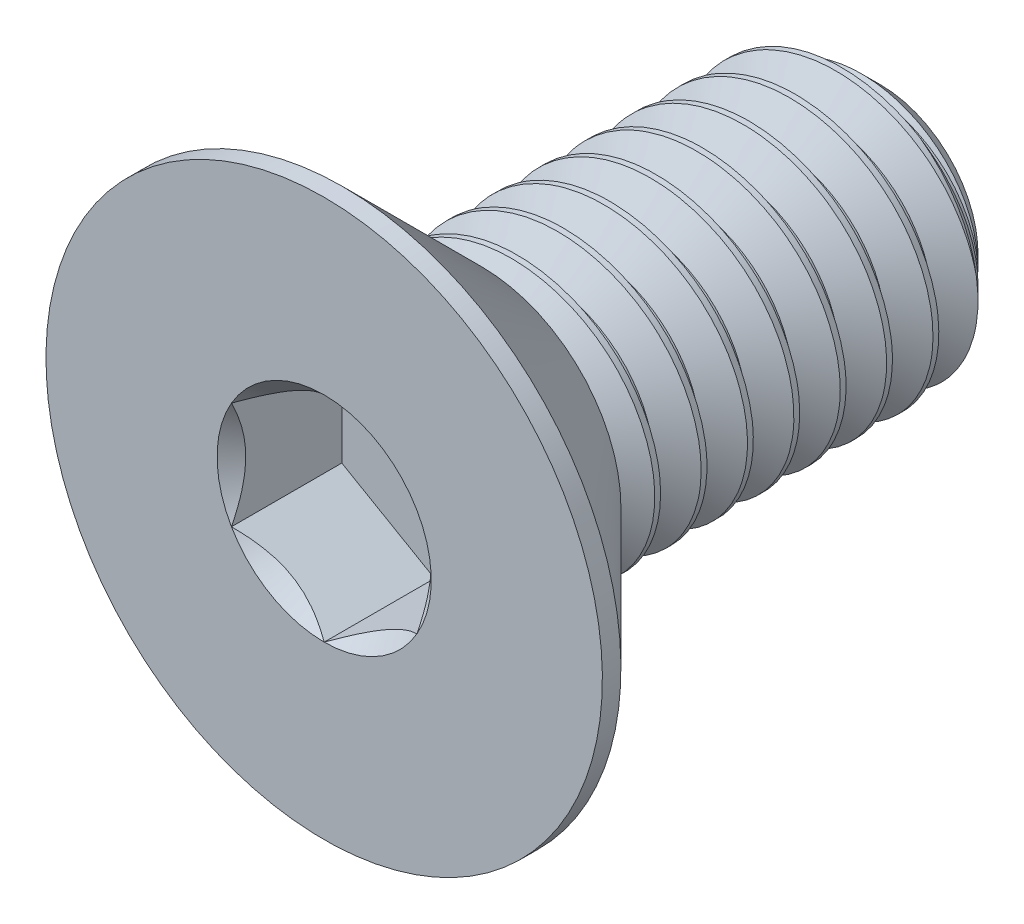
SolidWorks part; units mm, degrees
ref_plane "Front" through (0, 0, 0) normal (0, 0, 1) x (1, 0, 0)
ref_plane "Top" through (0, 0, 0) normal (0, 1, 0) x (1, 0, 0)
ref_plane "Right" through (0, 0, 0) normal (1, 0, 0) x (0, 0, -1)
sketch "Sketch1" plane through (0, 0, 0) normal (1, 0, 0) x (0, 0, -1)
  line L0 (-3, 3) -> (-2.8, 3) construction
  line L1 (-2.8, 3) -> (-1.3, 1.5) construction
  line L2 (-3, 1.5) -> (3, 1.5) construction
  line L3 (3, 1.5) -> (3, 0) construction
  line L4 (3, 0) -> (-3, 0) construction
  line L5 (-3, 0) -> (-3, 3) construction
  line L6 (-3, 3) -> (-3, -3) construction
  line L7 (3, 1.5) -> (3, -1.5) construction
  line L8 (-3, -3) -> (-2.8, -3) construction
  line L9 (-2.8, -3) -> (-1.3, -1.5) construction
  line L11 (-3, 1.5) -> (-3, 0) construction
  line L12 (-1.3, 1.5) -> (-1.3, 0) construction
  line L13 (2.9687, 1.5541) -> (3.2188, 1.1211) construction
  line L14 (3.2188, 1.1211) -> (3.4687, 1.5541) construction
  line L15 (3.4687, 1.5541) -> (2.9687, 1.5541) construction
  line L16 (3.2188, 1.5541) -> (3.2188, 1.5) construction
  line L17 (3.2188, 1.5) -> (3.2188, 1.1752) construction
  line L18 (3.2188, 1.1752) -> (3.2188, 1.1211) construction
  line L19 (3.2188, 1.5271) -> (3.4531, 1.5271) construction
  line L20 (3.2188, 1.5271) -> (2.9844, 1.5271) construction
  line L21 (3, 1.5) -> (3.4375, 1.5) construction
  line L22 (3.1875, 1.1752) -> (3.25, 1.1752) construction
  line L23 (3, -1.5) -> (-1.3, -1.5) construction
  point P10 (1.75, -1.5)
  point P24 (-1.3, 1.5)
  point P30 (0, 0)
  dimension "Head Diameter" = 6
  dimension "Head Height" = 1.7
  dimension "Length" = 6
  dimension "Countersink Angle" = 90
  dimension "Thread Pitch" = 0.5
  dimension "D2" = 0.0625
  dimension "Minimum Thread Length" = 4.3
  dimension "Thread Size" = 3
  dimension "D1" = 1.25
sketch "Sketch2" plane through (0, 0, 0) normal (0, 0, 1) x (1, 0, 0)
  line L1 (0, 1.1547) -> (-1, 0.5774) construction
  line L2 (-1, 0.5774) -> (-1, -0.5774) construction
  line L3 (-1, -0.5774) -> (0, -1.1547) construction
  line L4 (0, -1.1547) -> (1, -0.5774) construction
  line L5 (1, -0.5774) -> (1, 0.5774) construction
  line L6 (1, 0.5774) -> (0, 1.1547) construction
  circle A0 centre (0, 0) radius 1 construction
  dimension "Drive Size" = 2
sketch "Sketch3" plane through (0, 0, 0) normal (1, 0, 0) x (0, 0, -1)
  line L0 (-3, 1.5) -> (3, 1.5)
  line L1 (3, 1.5) -> (3, 0)
  line L2 (3, 0) -> (-3, 0)
  line L3 (-3, 0) -> (-3, 1.5)
revolve "Revolve1" add sketch "Sketch3" angle 360 about L4
chamfer "Chamfer1" distance 0.45 angle 45 1 edges at (0, 1.5, -3)
sketch "Sketch6" plane through (0, 0, 0) normal (1, 0, 0) x (0, 0, -1)
  line L0 (-3, 3) -> (-2.8, 3)
  line L1 (-2.8, 3) -> (-1.3, 1.5)
  line L2 (-1.3, 1.5) -> (-1.3, 0)
  line L3 (-1.3, 0) -> (-3, 0)
  line L4 (-3, 0) -> (-3, 3)
revolve "Revolve2" add sketch "Sketch6" angle 360 about L4
sketch "Sketch8" plane through (0, 0, 3) normal (0, 0, 1) x (1, 0, 0)
  line L0 (0, 1.1547) -> (-1, 0.5774) construction
  line L1 (1, 0.5774) -> (0, 1.1547) construction
  line L2 (1, -0.5774) -> (1, 0.5774) construction
  line L3 (0, -1.1547) -> (1, -0.5774) construction
  line L4 (-1, 0.5774) -> (-1, -0.5774) construction
  line L5 (-1, -0.5774) -> (0, -1.1547) construction
  line L6 (0, 1.1547) -> (-1, 0.5774)
  line L7 (1, 0.5774) -> (0, 1.1547)
  line L8 (1, -0.5774) -> (1, 0.5774)
  line L9 (0, -1.1547) -> (1, -0.5774)
  line L10 (-1, 0.5774) -> (-1, -0.5774)
  line L11 (-1, -0.5774) -> (0, -1.1547)
extrude "Cut-Extrude1" cut sketch "Sketch8" against normal blind 1.19
sketch "Sketch9" plane through (0, 0, 3) normal (0, 0, 1) x (1, 0, 0)
  circle A0 centre (0, 0) radius 1.1547
extrude "Cut-Extrude2" cut sketch "Sketch9" against normal up to next (1.19 mm away) draft 45
ref_plane "Plane1" through (0, 0, 1.3) normal (0, 0, 1) x (1, 0, 0)
split "Split1" trim tools "Plane1" bodies to split 124 resulting bodies 126 127
sketch "Sketch4" plane through (0, 0, -3) normal (0, 0, -1) x (-1, 0, 0)
  circle A0 centre (0, 0) radius 1.5 construction
  circle A1 centre (0, 0) radius 1.5
curve "Helix/Spiral1" pitch 0.5 height 4.8 turns 9.6
sketch "Sketch10" plane through (0, 0, 0) normal (1, 0, 0) x (0, 0, -1)
  line L0 (2.9844, 1.5271) -> (3.4531, 1.5271)
  line L1 (3.4531, 1.5271) -> (3.25, 1.1752)
  line L2 (3.25, 1.1752) -> (3.1875, 1.1752)
  line L3 (3.1875, 1.1752) -> (2.9844, 1.5271)
sweep "Cut-Sweep1" cut profiles "Sketch10" path "Helix/Spiral1"
equation "\"D2@Sketch1\" = \"Thread Pitch@Sketch1\" / 8"
equation "\"D4@Helix/Spiral1\"=\"Thread Pitch@Sketch1\""
equation "\"D3@Helix/Spiral1\"=\"Minimum Thread Length@Sketch1\"+\"Thread Pitch@Sketch1\""
equation "\"D1@Chamfer1\"=\"Thread Size@Sketch1\"*.15"
equation "\"D1@Cut-Extrude1\"=\"Head Height@Sketch1\"*.7"
equation "\"D1@Sketch1\"=\"Thread Pitch@Sketch1\"*2.5"
